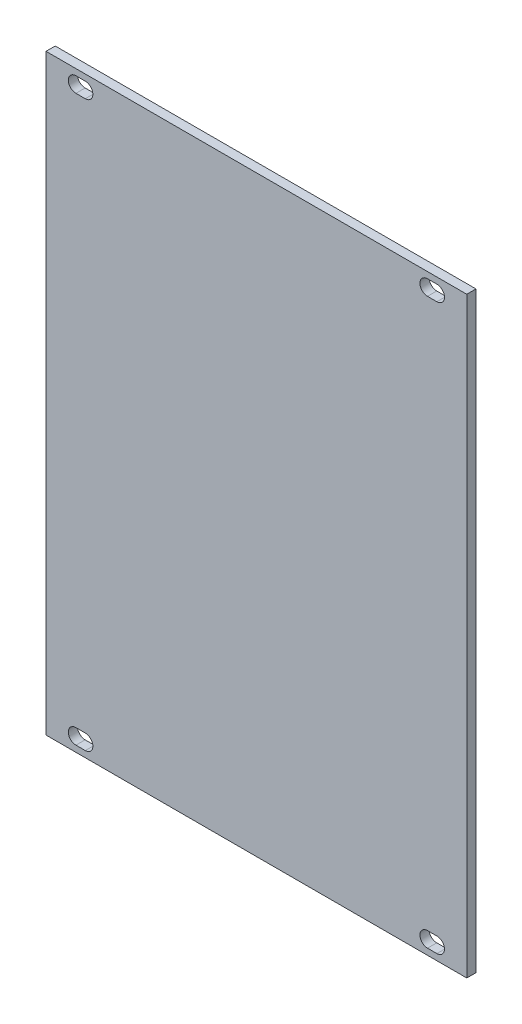
SolidWorks part; units mm, degrees
ref_plane "Front Plane" through (0, 0, 0) normal (0, 0, 1) x (1, 0, 0)
ref_plane "Top Plane" through (0, 0, 0) normal (0, 1, 0) x (1, 0, 0)
ref_plane "Right Plane" through (0, 0, 0) normal (1, 0, 0) x (0, 0, -1)
sketch "Sketch1" plane through (0, 0, 0) normal (0, 0, 1) x (1, 0, 0)
  line L0 (-38.15, 64.25) -> (-38.15, -64.25) construction
  line L1 (-45.65, 64.25) -> (45.65, 64.25)
  line L2 (-45.65, 64.25) -> (-45.65, -64.25)
  line L3 (-45.65, -64.25) -> (45.65, -64.25)
  line L4 (45.65, 64.25) -> (45.65, -64.25)
  line L5 (-45.65, 64.25) -> (45.65, -64.25) construction
  line L6 (-45.65, -64.25) -> (45.65, 64.25) construction
  line L7 (-45.65, 61.25) -> (45.65, 61.25) construction
  line L8 (-45.65, -61.25) -> (45.65, -61.25) construction
  line L9 (-39.166, -61.25) -> (-37.134, -61.25) construction
  line L10 (37.134, 61.25) -> (39.166, 61.25) construction
  line L11 (-39.166, -59.6) -> (-37.134, -59.6)
  line L12 (-39.166, -62.9) -> (-37.134, -62.9)
  line L13 (-39.166, 61.25) -> (-37.134, 61.25) construction
  line L14 (-39.166, 62.9) -> (-37.134, 62.9)
  line L15 (-39.166, 59.6) -> (-37.134, 59.6)
  line L16 (37.134, 62.9) -> (39.166, 62.9)
  line L17 (37.134, 59.6) -> (39.166, 59.6)
  line L18 (37.134, -61.25) -> (39.166, -61.25) construction
  line L19 (37.134, -59.6) -> (39.166, -59.6)
  line L20 (37.134, -62.9) -> (39.166, -62.9)
  line L21 (38.15, 64.25) -> (38.15, -64.25) construction
  arc A0 (-39.166, -59.6) -> (-39.166, -62.9) centre (-39.166, -61.25) ccw
  arc A1 (-37.134, -62.9) -> (-37.134, -59.6) centre (-37.134, -61.25) ccw
  arc A2 (-39.166, 62.9) -> (-39.166, 59.6) centre (-39.166, 61.25) ccw
  arc A3 (-37.134, 59.6) -> (-37.134, 62.9) centre (-37.134, 61.25) ccw
  arc A4 (37.134, 62.9) -> (37.134, 59.6) centre (37.134, 61.25) ccw
  arc A5 (39.166, 59.6) -> (39.166, 62.9) centre (39.166, 61.25) ccw
  arc A6 (37.134, -59.6) -> (37.134, -62.9) centre (37.134, -61.25) ccw
  arc A7 (39.166, -62.9) -> (39.166, -59.6) centre (39.166, -61.25) ccw
  point P0 (0, 0)
  point P8 (38.15, 61.25)
  point P18 (-38.15, -61.25)
  point P24 (-38.15, 61.25)
  point P34 (38.15, -61.25)
  point P42 (0, 0)
  point P43 (0, 0)
  dimension "D6" = 1.65
  dimension "D7" = 1.65
  dimension "D11" = 1.65
  dimension "D13" = 1.65
  dimension "D1" = 128.5
  dimension "D2" = 91.3
  dimension "D3" = 7.5
  dimension "D4" = 3
  dimension "D8" = 2.032
  dimension "D9" = 2.032
  dimension "D10" = 7.5
  dimension "D12" = 2.032
  dimension "D14" = 2.032
  dimension "D5" = 3
extrude "Boss-Extrude1" add sketch "Sketch1" along normal blind 2
